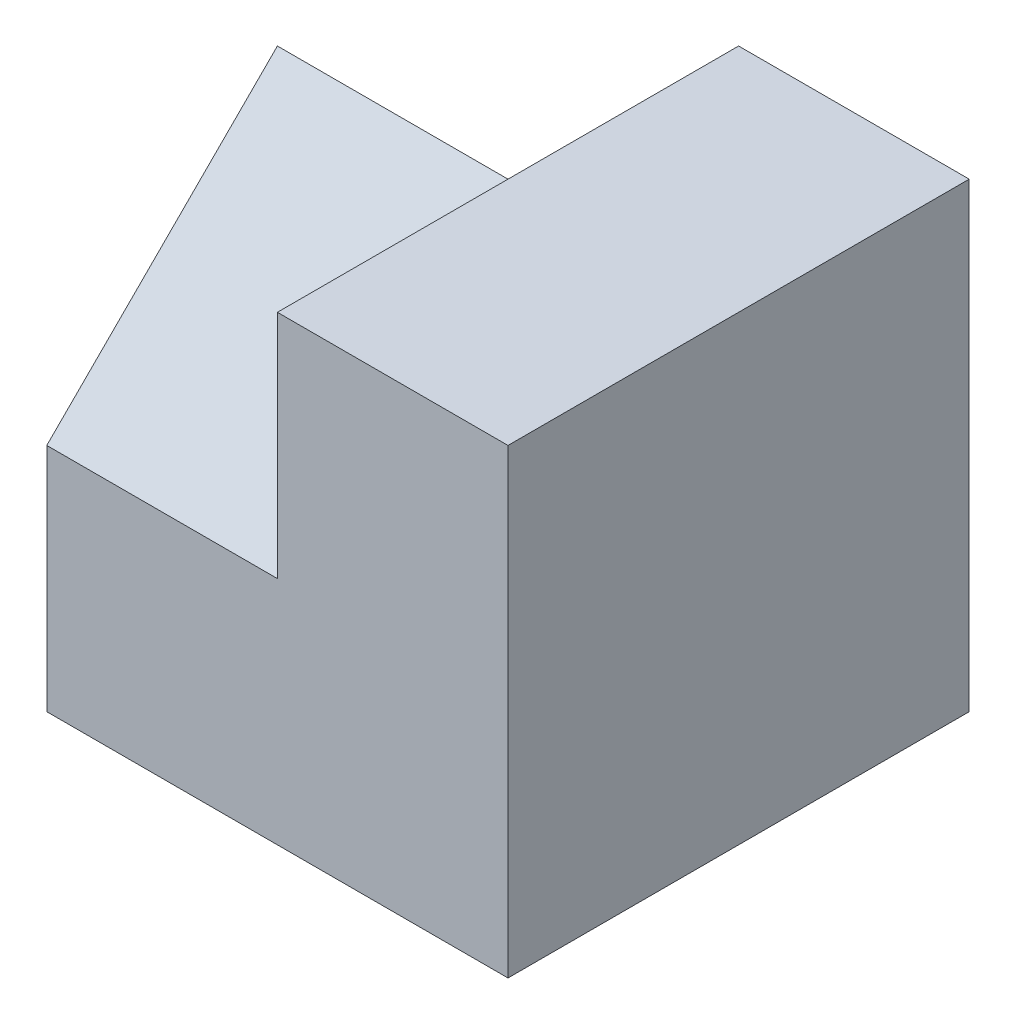
SolidWorks part; units mm, degrees
ref_plane "Front" through (0, 0, 0) normal (0, 0, 1) x (1, 0, 0)
ref_plane "Top" through (0, 0, 0) normal (0, 1, 0) x (1, 0, 0)
ref_plane "Right" through (0, 0, 0) normal (1, 0, 0) x (0, 0, -1)
sketch "Sketch1" plane through (0, 0, 0) normal (0, 1, 0) x (1, 0, 0)
  line L1 (-2, -2) -> (2, -2)
  line L2 (-2, -2) -> (-2, 2)
  line L3 (-2, 2) -> (2, 2)
  line L4 (2, -2) -> (2, 2)
  line L5 (-2, -2) -> (2, 2) construction
  line L6 (-2, 2) -> (2, -2) construction
  point P0 (0, 0)
  dimension "D1" = 4
  dimension "D2" = 4
extrude "Boss-Extrude1" add sketch "Sketch1" along normal blind 4
sketch "Sketch2" plane through (-2, 0, 0) normal (-1, 0, 0) x (0, 0, 1)
  line L0 (2, 2) -> (0, 4)
  line L1 (2, 4) -> (2, 0) construction
  line L2 (-2, 4) -> (2, 4) construction
  line L9 (-2, 0) -> (2, 0)
  line L10 (2, 0) -> (2, 4)
  line L11 (2, 4) -> (-2, 4)
  line L12 (-2, 4) -> (-2, 0)
  line L13 (-2, 0) -> (2, 0)
  line L14 (2, 0) -> (2, 4)
  line L15 (2, 4) -> (-2, 4)
  line L16 (-2, 4) -> (-2, 0)
  arc A0 (0, 4) -> (-2, 2) centre (-2, 4) cw
  dimension "D1" = 0
extrude "Cut-Extrude1" cut sketch "Sketch2" against normal blind 2
